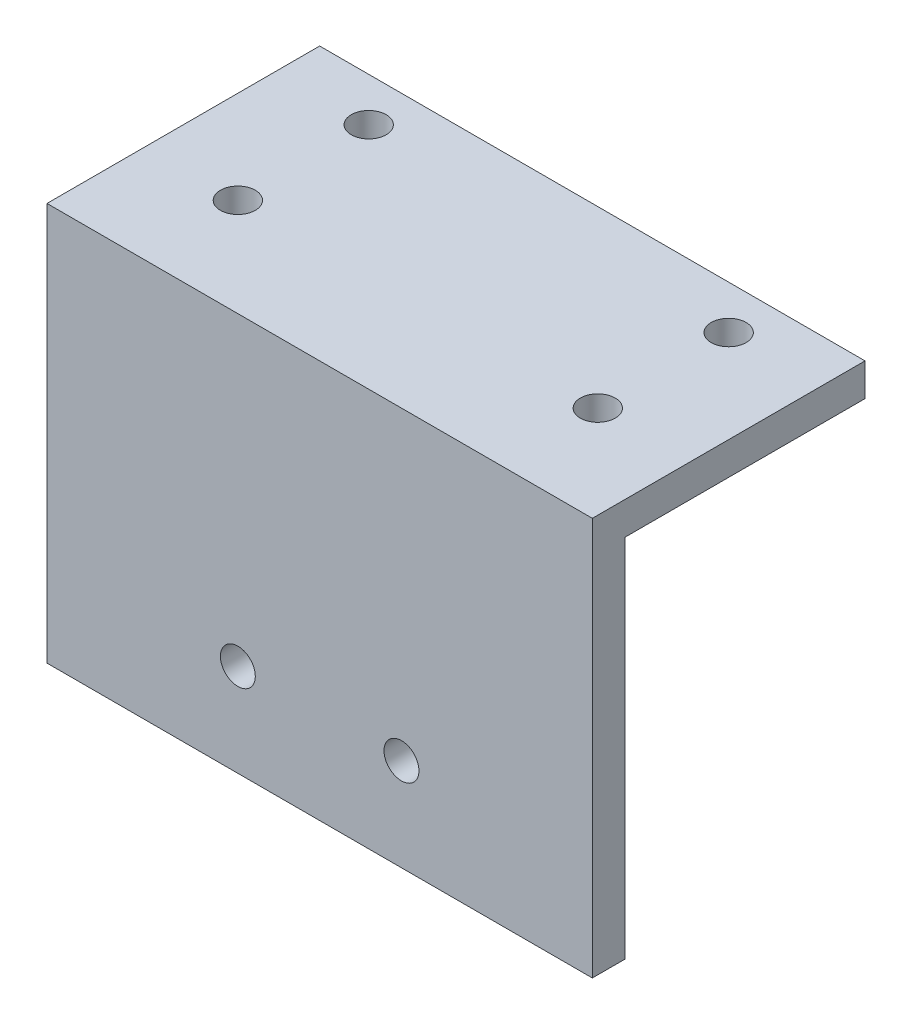
SolidWorks part; units mm, degrees
ref_plane "正面" through (0, 0, 0) normal (0, 0, 1) x (1, 0, 0)
ref_plane "平面" through (0, 0, 0) normal (0, 1, 0) x (1, 0, 0)
ref_plane "右側面" through (0, 0, 0) normal (1, 0, 0) x (0, 0, -1)
sketch "ｽｹｯﾁ1" plane through (0, 0, 0) normal (1, 0, 0) x (0, 0, -1)
  line L0 (0, 50) -> (25, 50)
  line L1 (25, 50) -> (25, 47)
  line L2 (25, 47) -> (3, 47)
  line L3 (3, 47) -> (3, 0)
  line L4 (3, 0) -> (0, 0)
  line L5 (0, 0) -> (0, 50)
  dimension "D1" = 25
  dimension "D2" = 50
  dimension "D3" = 3
  dimension "D4" = 3
extrude "ﾎﾞｽ - 押し出し1" add sketch "ｽｹｯﾁ1" along normal blind 50
sketch "ｽｹｯﾁ2" plane through (0, 47, 0) normal (0, -1, 0) x (1, 0, 0)
  line L0 (0, -9) -> (50, -9) construction
  line L1 (8.5, -3) -> (8.5, -25) construction
  line L2 (41.5, -3) -> (41.5, -25) construction
  line L3 (0, -21) -> (50, -21) construction
  line L5 (50, -3) -> (0, -3) construction
  line L6 (0, -3) -> (0, -25) construction
  line L7 (50, -3) -> (50, -25) construction
  line L8 (50, -25) -> (0, -25) construction
  circle A0 centre (8.5, -9) radius 1.6
  circle A1 centre (8.5, -21) radius 1.6
  circle A2 centre (41.5, -9) radius 1.6
  circle A3 centre (41.5, -21) radius 1.6
  dimension "D1" = 6
  dimension "D5" = 3.2
  dimension "D2" = 18
  dimension "D3" = 8.5
  dimension "D4" = 41.5
extrude "ｶｯﾄ - 押し出し1" cut sketch "ｽｹｯﾁ2" against normal through all
sketch "ｽｹｯﾁ3" plane through (0, 0, 0) normal (0, -1, 0) x (1, 0, 0)
  line L4 (0, 0) -> (0, -3)
  line L5 (0, -3) -> (50, -3)
  line L6 (50, -3) -> (50, 0)
  line L7 (50, 0) -> (0, 0)
  line L8 (0, 0) -> (0, -3)
  line L9 (0, -3) -> (50, -3)
  line L10 (50, -3) -> (50, 0)
  line L11 (50, 0) -> (0, 0)
  dimension "D1" = 0
extrude "ｶｯﾄ - 押し出し2" cut sketch "ｽｹｯﾁ3" against normal blind 13.5
sketch "ｽｹｯﾁ4" plane through (0, 0, 0) normal (0, 0, 1) x (1, 0, 0)
  line L0 (50, 13.5) -> (0, 13.5) construction
  line L1 (0, 26.5) -> (50, 26.5) construction
  line L2 (0, 26.5) -> (0, 17.5) construction
  line L3 (0, 17.5) -> (50, 17.5) construction
  line L4 (50, 26.5) -> (50, 17.5) construction
  line L5 (0, 26.5) -> (50, 17.5) construction
  line L6 (0, 17.5) -> (50, 26.5) construction
  line L8 (0, 50) -> (0, 13.5) construction
  line L17 (0, 22) -> (50, 22) construction
  circle A2 centre (17.5, 22) radius 1.6
  circle A3 centre (32.5, 22) radius 1.6
  point P0 (25, 22)
  point P25 (0, 22)
  dimension "D7" = 3.2
  dimension "D8" = 3.2
  dimension "D1" = 9
  dimension "D4" = 4
  dimension "D11" = 7.5
  dimension "D12" = 7.5
extrude "ｶｯﾄ - 押し出し3" cut sketch "ｽｹｯﾁ4" against normal through all
